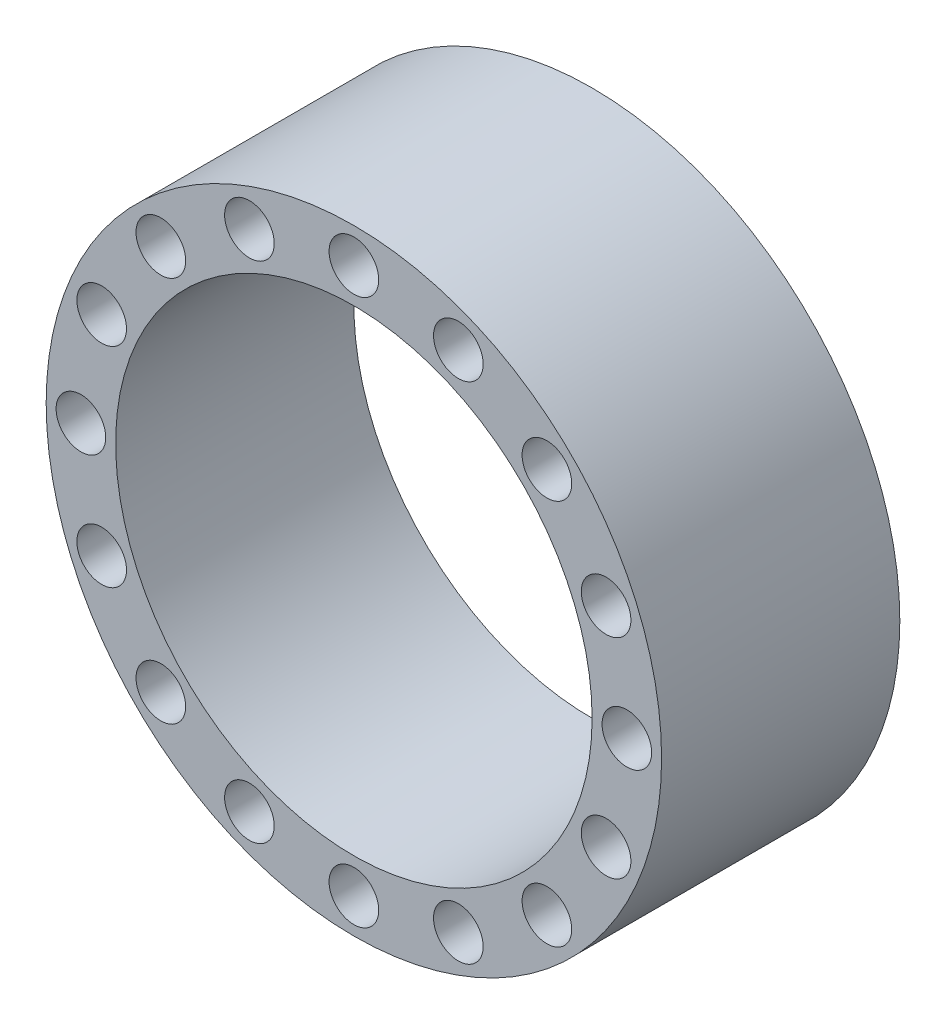
SolidWorks part; units mm, degrees
material "ABS"
ref_plane "正面" through (0, 0, 0) normal (0, 0, 1) x (1, 0, 0)
ref_plane "平面" through (0, 0, 0) normal (0, 1, 0) x (1, 0, 0)
ref_plane "右側面" through (0, 0, 0) normal (1, 0, 0) x (0, 0, -1)
sketch "ｽｹｯﾁ1" plane through (0, 0, 0) normal (0, 0, 1) x (1, 0, 0)
  circle A0 centre (0, 0) radius 31
  circle A1 centre (0, 0) radius 24
  dimension "D1" = 62
  dimension "D2" = 48
extrude "ﾎﾞｽ - 押し出し1" add sketch "ｽｹｯﾁ1" along normal blind 24
hole_wizard "M3 すきま穴1" positions "ｽｹｯﾁ2" profile "ｽｹｯﾁ3" hole size "M3" standard "JIS" end condition through all
sketch "ｽｹｯﾁ2" plane through (0, 0, 24) normal (0, 0, 1) x (1, 0, 0)
  circle A0 centre (0, 0) radius 27.5 construction
  circle A1 centre (0, 0) radius 31 construction
  point P0 (0, 27.5)
  dimension "D1" = 3.5
sketch "ｽｹｯﾁ3" plane through (0, 27.5, 24) normal (1, 0, 0) x (0, -1, 0)
  line L0 (0, 0) -> (0, 24)
  line L1 (0, 24) -> (1.7, 24)
  line L2 (1.7, 24) -> (1.7, 0)
  line L5 (1.7, 0) -> (0, 0)
  line L11 (0, -6.35) -> (0, 107.95) construction
  dimension "通し穴の直径" = 3.4
  dimension "通し穴の深さ" = 24
sketch "ｽｹｯﾁ5" plane through (0, 0, 0) normal (1, 0, 0) x (0, 0, -1)
  line L0 (-4.5, -6) -> (-19.5, -6) construction
  line L1 (-4.5, -7.5) -> (-19.5, -7.5)
  line L2 (-4.5, -4.5) -> (-19.5, -4.5)
  line L3 (0, -24) -> (0, 24) construction
  line L4 (-24, 0) -> (0, 0) construction
  line L5 (-24, 24) -> (-24, -24) construction
  line L6 (-4.5, 6) -> (-19.5, 6) construction
  line L7 (-4.5, 7.5) -> (-19.5, 7.5)
  line L8 (-4.5, 4.5) -> (-19.5, 4.5)
  arc A0 (-4.5, -7.5) -> (-4.5, -4.5) centre (-4.5, -6) ccw
  arc A1 (-19.5, -4.5) -> (-19.5, -7.5) centre (-19.5, -6) ccw
  arc A2 (-4.5, 7.5) -> (-4.5, 4.5) centre (-4.5, 6) cw
  arc A3 (-19.5, 4.5) -> (-19.5, 7.5) centre (-19.5, 6) cw
  point P3 (-12, -6)
  point P17 (-12, 6)
  dimension "D2" = 1.5
  dimension "D1" = 12
  dimension "D3" = 15
  dimension "D4" = 6
extrude "ｶｯﾄ - 押し出し1" [suppressed] cut sketch "ｽｹｯﾁ5" against normal through all both and the other way through all
pattern_circular "円形ﾊﾟﾀｰﾝ2" [suppressed] count 8 over 360
sketch "ｽｹｯﾁ6" plane through (0, 0, 24) normal (0, 0, 1) x (1, 0, 0)
  line L1 (0, 41.0122) -> (41.0122, 0)
  line L2 (0, 41.0122) -> (-41.0122, 0)
  line L3 (-41.0122, 0) -> (0, -41.0122)
  line L4 (41.0122, 0) -> (0, -41.0122)
  line L5 (0, 41.0122) -> (0, -41.0122) construction
  line L6 (-41.0122, 0) -> (41.0122, 0) construction
  circle A0 centre (0, 0) radius 31 construction
  point P0 (0, 0)
  circle M13 centre (0, 0) radius 31
  dimension "D1" = 29
extrude "ｶｯﾄ - 押し出し2" [suppressed] cut sketch "ｽｹｯﾁ6" against normal through all contours L3 M13 | L1 M13
sketch "ｽｹｯﾁ7" plane through (0, 0, 24) normal (0, 0, 1) x (1, 0, 0)
  line L0 (0, 25) -> (0, 0) construction
  circle A0 centre (0, 27.5) radius 2.5
  dimension "D1" = 5
ref_plane "平面1" through (0, 0, 12) normal (0, 0, -1) x (-1, 0, 0)
extrude "ｶｯﾄ - 押し出し3" cut sketch "ｽｹｯﾁ7" against normal blind 6
pattern_circular "円形ﾊﾟﾀｰﾝ3" count 16 over 360 about axis through (0, 0, 0) along (0, 0, 1) of "ｶｯﾄ - 押し出し3", "M3 すきま穴1"
mirror "ﾐﾗｰ1" about plane through (0, 0, 12) normal (0, 0, -1) of "円形ﾊﾟﾀｰﾝ3", "ｶｯﾄ - 押し出し3"
